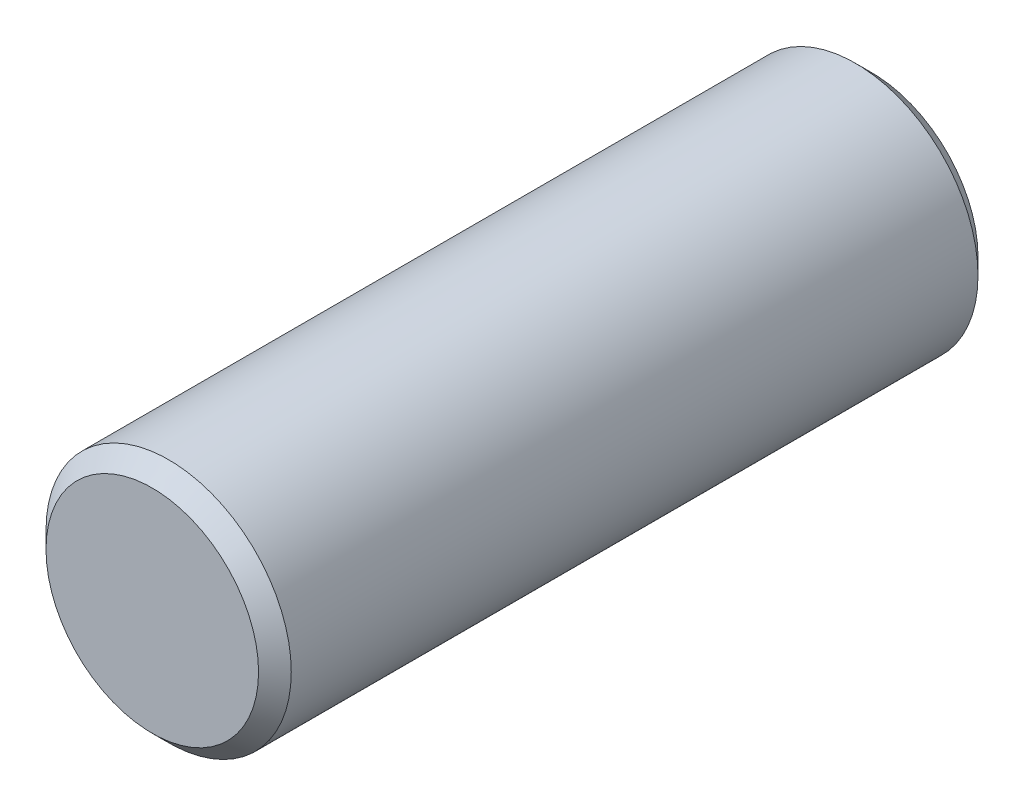
SolidWorks part; units mm, degrees
ref_plane "Ön Düzlem" through (0, 0, 0) normal (0, 0, 1) x (1, 0, 0)
ref_plane "Üst Düzlem" through (0, 0, 0) normal (0, 1, 0) x (1, 0, 0)
ref_plane "Sağ Düzlem" through (0, 0, 0) normal (1, 0, 0) x (0, 0, -1)
sketch "Sketch1" plane through (0, 0, 0) normal (0, 0, 1) x (1, 0, 0)
  circle A0 centre (0, 0) radius 7.5
  dimension "D1" = 15
extrude "Boss-Extrude1" add sketch "Sketch1" along normal blind 44
chamfer "Chamfer1" distance 1 angle 45 1 edges at (7.5, 0, 0)
chamfer "Chamfer2" distance 1 angle 45 1 edges at (7.5, 0, 44)
